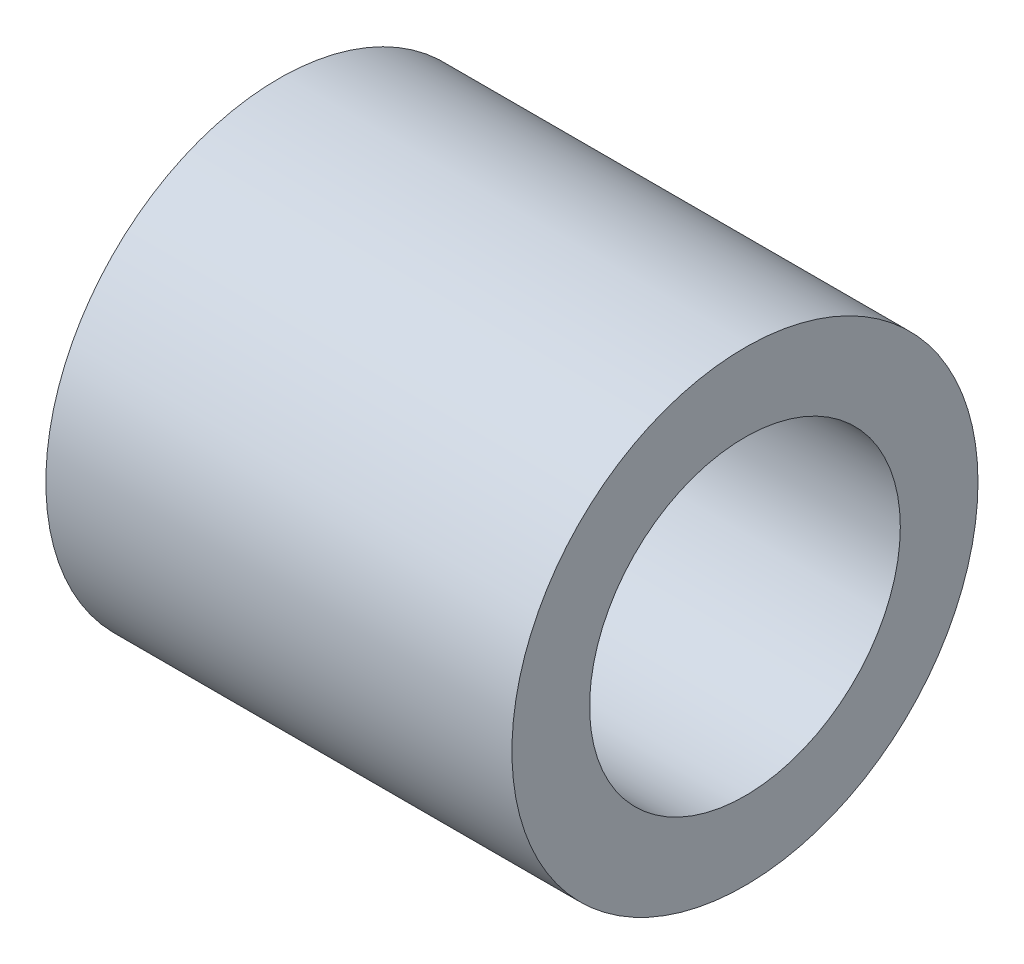
SolidWorks part; units mm, degrees
material "黄铜"
ref_plane "前视基准面" through (0, 0, 0) normal (0, 0, 1) x (1, 0, 0)
ref_plane "上视基准面" through (0, 0, 0) normal (0, 1, 0) x (1, 0, 0)
ref_plane "右视基准面" through (0, 0, 0) normal (1, 0, 0) x (0, 0, -1)
sketch "草图1" plane through (0, 0, 0) normal (1, 0, 0) x (0, 0, -1)
  circle A0 centre (0, 0) radius 6
  circle A1 centre (0, 0) radius 9
  dimension "D1" = 12
  dimension "D2" = 18
extrude "凸台-拉伸1" add sketch "草图1" against normal blind 18
